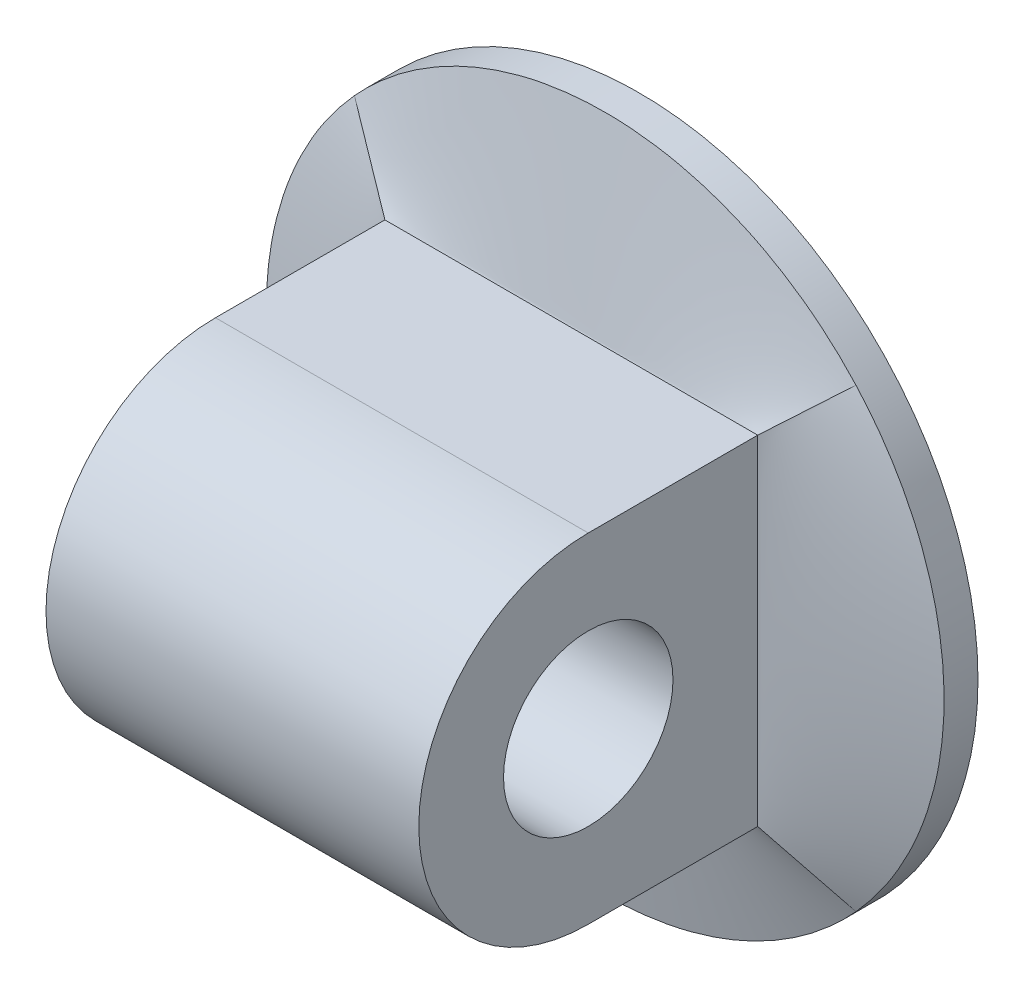
SolidWorks part; units mm, degrees
ref_plane "Front" through (0, 0, 0) normal (0, 0, 1) x (1, 0, 0)
ref_plane "Top" through (0, 0, 0) normal (0, 1, 0) x (1, 0, 0)
ref_plane "Right" through (0, 0, 0) normal (1, 0, 0) x (0, 0, -1)
sketch "Sketch1" plane through (0, 0, 0) normal (0, 0, 1) x (1, 0, 0)
  circle A0 centre (0, 0) radius 25.4
  circle A1 centre (0, 0) radius 19.05
  dimension "D1" = 6.35
  dimension "D2" = 38.1
extrude "Boss-Extrude1" add sketch "Sketch1" along normal blind 2.54
sketch "Sketch2" plane through (0, 0, 0) normal (1, 0, 0) x (0, 0, -1)
  line L0 (-2.54, 19.05) -> (-2.54, -19.05) construction
  circle A0 centre (-17.78, 0) radius 6.35
  dimension "D1" = 12.7
  dimension "D2" = 15.24
sketch "Sketch3" plane through (0, 0, 2.54) normal (0, 0, 1) x (1, 0, 0)
  circle A1 centre (0, 0) radius 25.4
  circle A2 centre (0, 0) radius 25.4
  dimension "D1" = 0
ref_plane "Plane2" through (0, 0, 5.08) normal (0, 0, 1) x (1, 0, 0)
sketch "Sketch4" plane through (0, 0, 5.08) normal (0, 0, 1) x (1, 0, 0)
  line L1 (-13.97, 12.7) -> (13.97, 12.7)
  line L2 (-13.97, 12.7) -> (-13.97, -12.7)
  line L3 (-13.97, -12.7) -> (13.97, -12.7)
  line L4 (13.97, 12.7) -> (13.97, -12.7)
  line L5 (-13.97, 12.7) -> (13.97, -12.7) construction
  line L6 (-13.97, -12.7) -> (13.97, 12.7) construction
  point P0 (0, 0)
  dimension "D1" = 25.4
  dimension "D2" = 27.94
loft "Loft1" add profiles "Sketch3", "Sketch4"
sketch "Sketch5" plane through (0, 0, 5.08) normal (0, 0, 1) x (1, 0, 0)
  line L4 (13.97, -12.7) -> (13.97, 12.7)
  line L5 (13.97, 12.7) -> (-13.97, 12.7)
  line L6 (-13.97, 12.7) -> (-13.97, -12.7)
  line L7 (-13.97, -12.7) -> (13.97, -12.7)
  line L8 (13.97, -12.7) -> (13.97, 12.7)
  line L9 (13.97, 12.7) -> (-13.97, 12.7)
  line L10 (-13.97, 12.7) -> (-13.97, -12.7)
  line L11 (-13.97, -12.7) -> (13.97, -12.7)
  dimension "D1" = 0
extrude "Boss-Extrude2" add sketch "Sketch5" along normal blind 25.4
extrude "Cut-Extrude1" cut sketch "Sketch2" against normal through all and the other way through all
sketch "Sketch10" plane through (13.97, 0, 0) normal (1, 0, 0) x (0, 0, -1)
  line L0 (-30.48, 12.7) -> (-5.08, 12.7) construction
  line L1 (-30.48, -12.7) -> (-30.48, 12.7) construction
  line L3 (-30.48, 12.7) -> (-17.78, 12.7)
  line L4 (-30.48, 0) -> (-30.48, 12.7)
  arc A0 (-17.78, 12.7) -> (-30.48, 0) centre (-17.78, 0) ccw
extrude "Cut-Extrude4" cut sketch "Sketch10" against normal through all
mirror "Mirror2" about plane through (0, 0, 0) normal (0, 1, 0) of "Cut-Extrude4"
